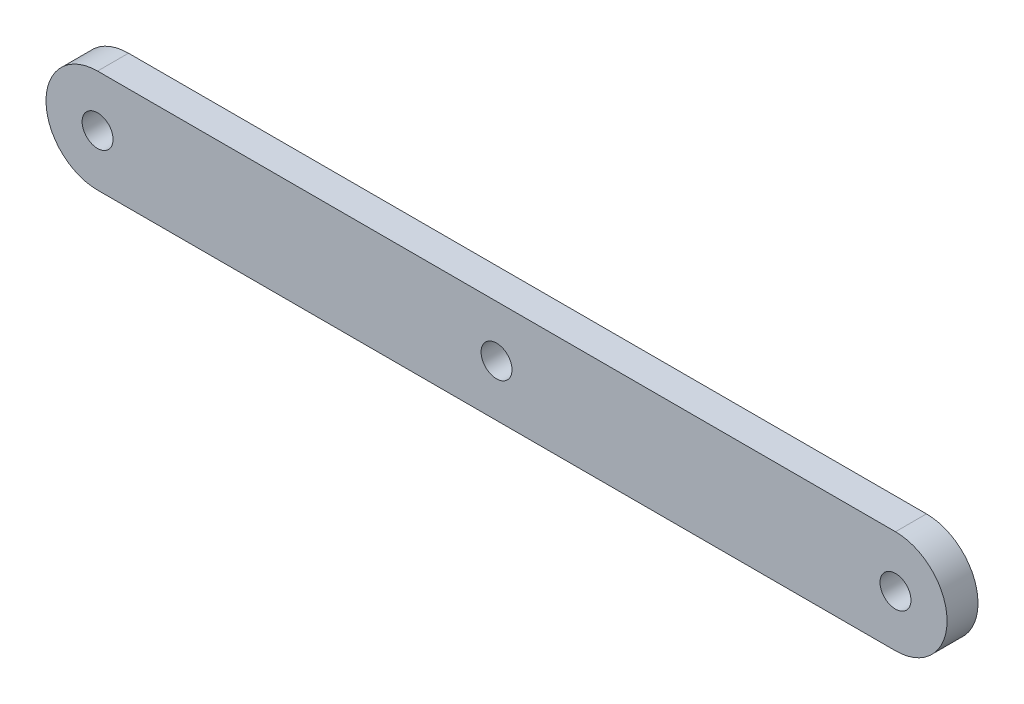
SolidWorks part; units mm, degrees
ref_plane "前基準面" through (0, 0, 0) normal (0, 0, 1) x (1, 0, 0)
ref_plane "上基準面" through (0, 0, 0) normal (0, 1, 0) x (1, 0, 0)
ref_plane "右基準面" through (0, 0, 0) normal (1, 0, 0) x (0, 0, -1)
sketch "草圖1" plane through (0, 0, 0) normal (0, 0, 1) x (1, 0, 0)
  line L0 (-19.3421, 0) -> (19.3421, 0) construction
  line L1 (-19.3421, 2.5) -> (19.3421, 2.5)
  line L2 (-19.3421, -2.5) -> (19.3421, -2.5)
  arc A0 (-19.3421, 2.5) -> (-19.3421, -2.5) centre (-19.3421, 0) ccw
  arc A1 (19.3421, -2.5) -> (19.3421, 2.5) centre (19.3421, 0) ccw
  circle A2 centre (-19.3421, 0) radius 0.75
  circle A3 centre (19.3421, 0) radius 0.75
  circle A4 centre (0, 0) radius 0.75
  point P3 (0, 0)
  dimension "D2" = 2.5
  dimension "D3" = 1.5
  dimension "D1" = 38.6842
extrude "填料-伸長1" add sketch "草圖1" along normal mid plane 1.5
